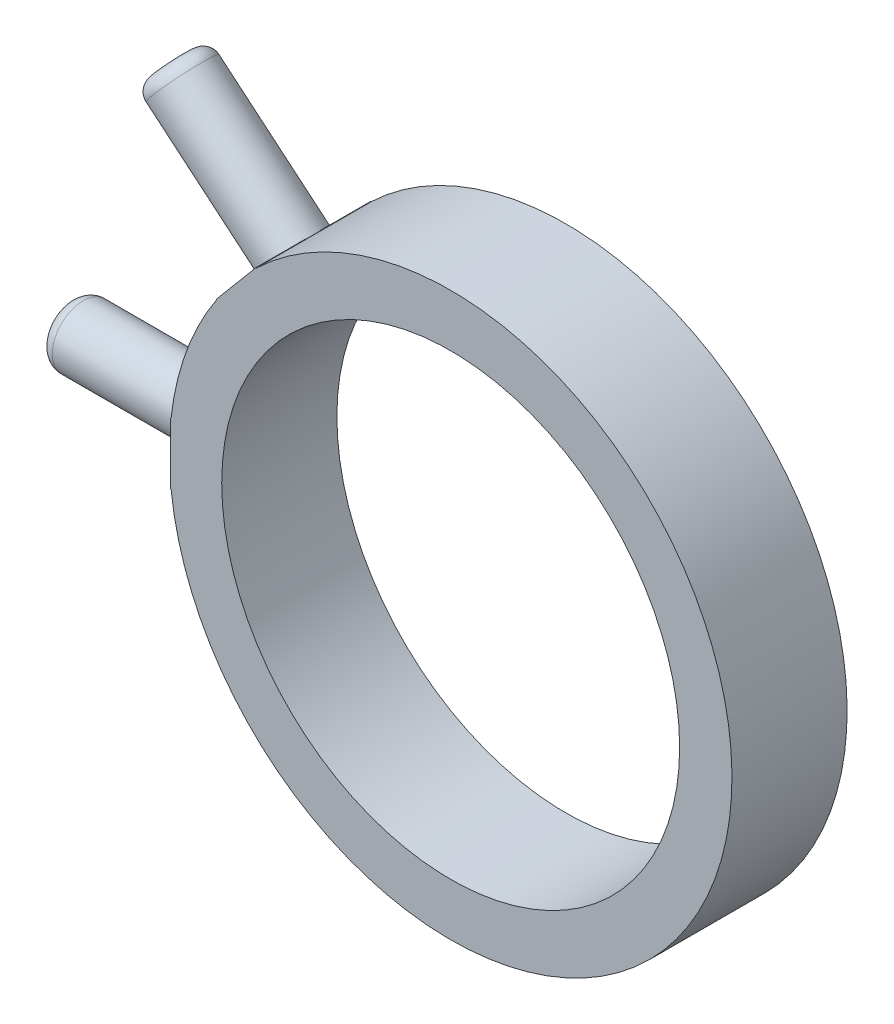
SolidWorks part; units mm, degrees
ref_plane "Plan de face" through (0, 0, 0) normal (0, 0, 1) x (1, 0, 0)
ref_plane "Plan de dessus" through (0, 0, 0) normal (0, 1, 0) x (1, 0, 0)
ref_plane "Plan de droite" through (0, 0, 0) normal (1, 0, 0) x (0, 0, -1)
sketch "Esquisse1" plane through (0, 0, 0) normal (0, 0, 1) x (1, 0, 0)
  line L0 (0, 0) -> (-17.5, 0)
  line L6 (-33.5, 2.35) -> (-21.5, 2.35)
  line L7 (-33.5, 2.35) -> (-33.5, -2.35)
  line L8 (-33.5, -2.35) -> (-21.5, -2.35)
  line L10 (-27.173, 19.7332) -> (-24.1519, 23.3336)
  line L12 (-21.5, 2.35) -> (-21.3712, 2.35)
  line L13 (-21.5, -2.35) -> (-21.3712, -2.35)
  line L15 (-24.1519, 23.3336) -> (-14.8607, 15.5373)
  line L18 (-27.173, 19.7332) -> (-17.8818, 11.9369)
  circle A0 centre (0, 0) radius 17.5
  arc A1 (-21.3712, -2.35) -> (-14.8607, 15.5373) centre (0, 0) ccw
  arc A2 (-17.8818, 11.9369) -> (-21.3712, 2.35) centre (0, 0) ccw
  point P4 (-27.9938, 0.5162)
  point P6 (-21.4725, 0)
  point P8 (-27.5, 0)
  point P20 (0, 0)
  dimension "D1" = 35
  dimension "D2" = 43
  dimension "D4" = 4.7
extrude "Boss.-Extru.1" add sketch "Esquisse1" along normal blind 8.8 contours A0 | A1 L15 L10 L18 A2 L12 L6 L7 L8 L13
sketch "Esquisse4" plane through (-25.6625, 21.5334, 0) normal (-0.766, 0.6428, 0) x (0, 0, 1)
  line L0 (0, 0) -> (8.8, 0) construction
  line L1 (8.8, -2.35) -> (8.8, 2.35) construction
  circle A0 centre (4.4, 0) radius 2.35
  circle A1 centre (4.4, 0) radius 6.3732
extrude "Enlèv. mat.-Extru.1" cut sketch "Esquisse4" against normal blind 12.1 contours A0 | A1
sketch "Esquisse5" plane through (-33.5, 0, 0) normal (-1, 0, 0) x (0, 0, 1)
  line L0 (0, 0) -> (8.8, 0) construction
  line L1 (8.8, 2.35) -> (8.8, -2.35) construction
  circle A0 centre (4.4, 0) radius 2.35
  circle A1 centre (4.4, 0) radius 10.6894
extrude "Enlèv. mat.-Extru.2" cut sketch "Esquisse5" against normal blind 12.1
fillet "Congé1" radius 1 2 edges at (-27.173, 19.7332, 4.4) (-33.5, 0, 6.75)
